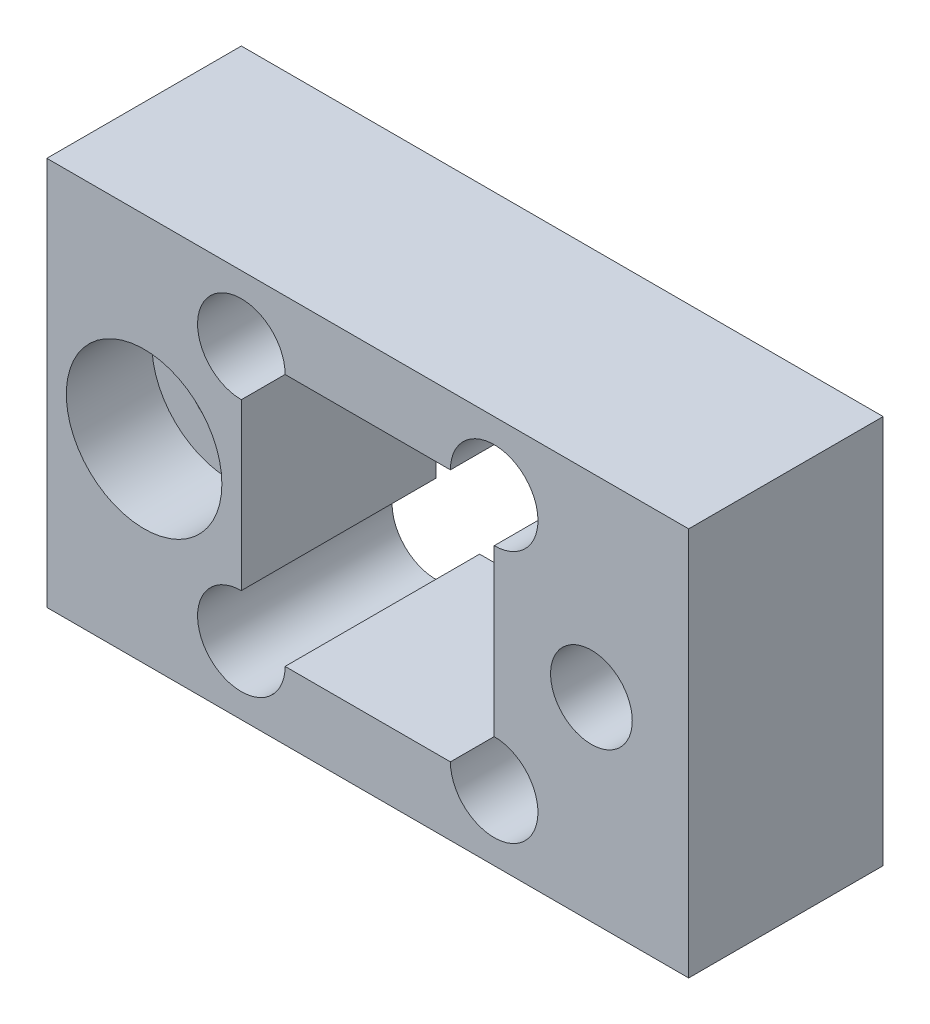
SolidWorks part; units mm, degrees
ref_plane "Ebene vorne" through (0, 0, 0) normal (0, 0, 1) x (1, 0, 0)
ref_plane "Ebene oben" through (0, 0, 0) normal (0, 1, 0) x (1, 0, 0)
ref_plane "Ebene rechts" through (0, 0, 0) normal (1, 0, 0) x (0, 0, -1)
sketch "Skizze1" plane through (0, 0, 0) normal (0, 0, 1) x (1, 0, 0)
  line L1 (-6.5, 6.5) -> (6.5, 6.5)
  line L2 (-6.5, 6.5) -> (-6.5, -6.5)
  line L3 (-6.5, -6.5) -> (6.5, -6.5)
  line L4 (6.5, 6.5) -> (6.5, -6.5)
  line L5 (-6.5, 6.5) -> (6.5, -6.5) construction
  line L6 (-6.5, -6.5) -> (6.5, 6.5) construction
  line L7 (-16.5, -10) -> (16.5, -10)
  line L8 (-16.5, -10) -> (-16.5, 10)
  line L9 (-16.5, 10) -> (16.5, 10)
  line L10 (16.5, -10) -> (16.5, 10)
  point P0 (0, 0)
  point P10 (-16.5, 0)
  dimension "D1" = 13
  dimension "D2" = 10
  dimension "D3" = 20
  dimension "D4" = 10
extrude "Aufsatz-Linear austragen1" add sketch "Skizze1" along normal blind 10
hole_wizard "Stirnsenkung für M4 Zylinderschraube mit Innensechskant1" positions "Skizze3" profile "Skizze4" counterbore size "M4" standard "DIN" end condition through all
sketch "Skizze3" plane through (0, 0, 10) normal (0, 0, 1) x (1, 0, 0)
  line L0 (-6.5, 0) -> (-16.5, 0) construction
  line L1 (-6.5, 6.5) -> (-6.5, -6.5) construction
  line L2 (-16.5, 10) -> (-16.5, -10) construction
  point P0 (-11.5, 0)
sketch "Skizze4" plane through (-11.5, 0, 10) normal (1, 0, 0) x (0, -1, 0)
  line L0 (0, 0) -> (0, 10)
  line L1 (0, 10) -> (2.25, 10)
  line L3 (2.25, 10) -> (2.25, 4.4)
  line L4 (2.25, 4.4) -> (4, 4.4)
  line L5 (4, 4.4) -> (4, 0)
  line L7 (4, 0) -> (0, 0)
  line L11 (0, -6.35) -> (0, 107.95) construction
  dimension "Bohrerdurchmesser" = 4.5
  dimension "Bohrungstiefe" = 10
  dimension "Senkdurchmesser2" = 8
  dimension "Senktiefe2" = 4.4
sketch "Skizze8" plane through (0, 0, 10) normal (0, 0, 1) x (1, 0, 0)
  circle A0 centre (-6.5, 6.5) radius 2.25
  circle A1 centre (-6.5, -6.5) radius 2.25
  circle A2 centre (6.5, -6.5) radius 2.25
  circle A3 centre (6.5, 6.5) radius 2.25
  dimension "D1" = 4.5
extrude "Schnitt-Linear austragen1" cut sketch "Skizze8" against normal through all
hole_wizard "M5 Gewindebohrung1" positions "Skizze9" profile "Skizze10" tap size "M5" standard "DIN" end condition through all
sketch "Skizze9" plane through (0, 0, 10) normal (0, 0, 1) x (1, 0, 0)
  line L0 (6.5, 0) -> (16.5, 0) construction
  line L1 (6.5, -4.25) -> (6.5, 4.25) construction
  line L2 (16.5, -10) -> (16.5, 10) construction
  point P0 (11.5, 0)
  point P9 (0, 0)
sketch "Skizze10" plane through (11.5, 0, 10) normal (1, 0, 0) x (0, -1, 0)
  line L0 (0, 0) -> (0, 10)
  line L1 (0, 10) -> (2.1, 10)
  line L2 (2.1, 10) -> (2.1, 0)
  line L5 (2.1, 0) -> (0, 0)
  line L11 (0, -6.35) -> (0, 107.95) construction
  dimension "Bohrerdurchmesser" = 4.2
  dimension "Bohrungstiefe" = 10
cosmetic thread "Bohrungsgewinde1" parameters "D2"=5
